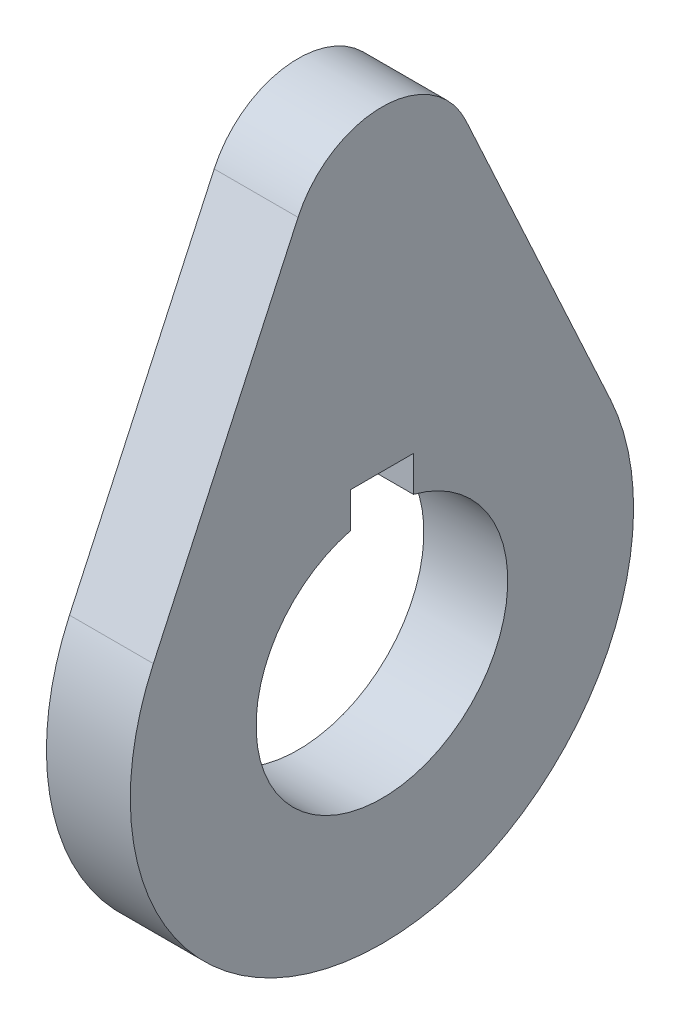
SolidWorks part; units mm, degrees
material "Plain Carbon Steel"
ref_plane "Front Plane" through (0, 0, 0) normal (0, 0, 1) x (1, 0, 0)
ref_plane "Top Plane" through (0, 0, 0) normal (0, 1, 0) x (1, 0, 0)
ref_plane "Right Plane" through (0, 0, 0) normal (1, 0, 0) x (0, 0, -1)
sketch "Sketch1" plane through (0, 0, 0) normal (1, 0, 0) x (0, 0, -1)
  circle A0 centre (0, 0) radius 19.05
  circle A1 centre (0, 0) radius 38.1
extrude "Boss-Extrude1" add sketch "Sketch1" along normal blind 12.7
sketch "Sketch2" plane through (12.7, 0, 0) normal (1, 0, 0) x (0, 0, -1)
  line L0 (-4.7625, 19.05) -> (4.7625, 19.05) construction
  line L1 (-4.7625, 23.8125) -> (4.7625, 23.8125)
  line L2 (-4.7625, 23.8125) -> (-4.7625, 14.2875)
  line L3 (-4.7625, 14.2875) -> (4.7625, 14.2875)
  line L4 (4.7625, 23.8125) -> (4.7625, 14.2875)
  line L5 (4.7625, 19.05) -> (0, 23.8125) construction
  line L6 (0, 23.8125) -> (0, 19.05) construction
  line L7 (0, 19.05) -> (0, 0) construction
  dimension "D1" = 19.05
  dimension "D2" = 9.525
  dimension "D3" = 9.525
extrude "Cut-Extrude1" cut sketch "Sketch2" against normal through all
sketch "Sketch3" plane through (12.7, 0, 0) normal (1, 0, 0) x (0, 0, -1)
  line L0 (-34.6058, 15.9388) -> (-12.7, 63.5)
  line L1 (-12.7, 63.5) -> (12.7, 63.5) construction
  line L2 (12.7, 63.5) -> (34.6058, 15.9388)
  line L3 (-34.6058, 15.9388) -> (34.6058, 15.9388) construction
  circle A0 centre (0, 0) radius 38.1 construction
  arc A1 (-34.6058, 15.9388) -> (34.6058, 15.9388) centre (0, 0) cw
  arc A2 (-12.7, 63.5) -> (12.7, 63.5) centre (0, 57.6506) cw
  dimension "D1" = 25.4
  dimension "D2" = 63.5
extrude "Boss-Extrude2" add sketch "Sketch3" against normal up to surface (12.7 mm away) up to face at (0, 0, -38.1)
